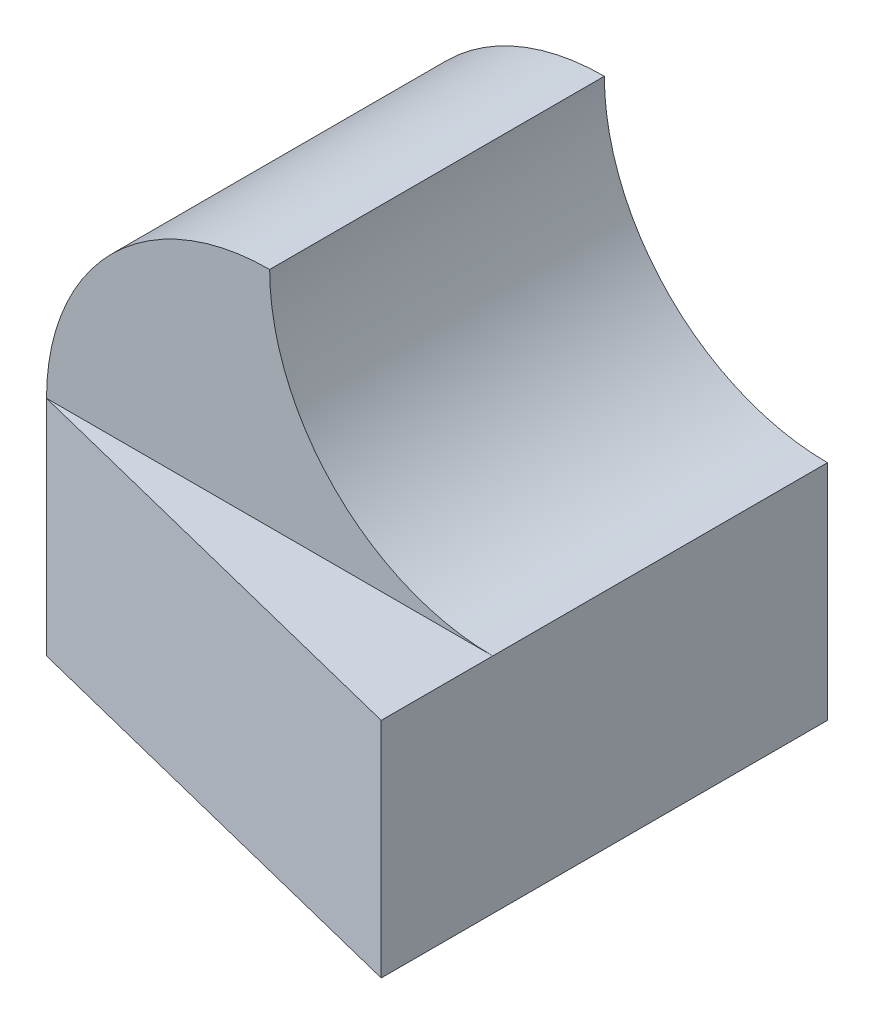
SolidWorks part; units mm, degrees
ref_plane "Front" through (0, 0, 0) normal (0, 0, 1) x (1, 0, 0)
ref_plane "Top" through (0, 0, 0) normal (0, 1, 0) x (1, 0, 0)
ref_plane "Right" through (0, 0, 0) normal (1, 0, 0) x (0, 0, -1)
sketch "Sketch1" plane through (0, 0, 0) normal (0, 0, 1) x (1, 0, 0)
  line L0 (0, 0) -> (4, 0)
  line L1 (4, 0) -> (4, 2)
  line L2 (0, 2) -> (0, 0)
  arc A0 (4, 2) -> (2, 4) centre (4, 4) cw
  arc A1 (2, 4) -> (0, 2) centre (2, 2) ccw
  point P8 (1.9827, 3.9999)
  dimension "D4" = 2
  dimension "D5" = 2
  dimension "D1" = 2
  dimension "D2" = 2
  dimension "D3" = 4
  dimension "D6" = 2
  dimension "D7" = 2
extrude "Boss-Extrude1" add sketch "Sketch1" along normal blind 3
sketch "Sketch2" plane through (0, 0, 0) normal (0, -1, 0) x (1, 0, 0)
  line L0 (0, 3) -> (4, 4)
  line L1 (4, 4) -> (4, 3)
  line L2 (4, 3) -> (0, 3)
  point P3 (4, 3.9884)
  dimension "D1" = 1
extrude "Boss-Extrude2" add sketch "Sketch2" against normal blind 2
sketch "Sketch4" plane through (0, 0, 0) normal (0, 0, -1) x (-1, 0, 0)
  line L0 (-2, 0) -> (0, 2)
  line L1 (0, 0) -> (-4, 0) construction
  line L2 (0, 2) -> (0, 0)
  line L3 (0, 0) -> (-2, 0)
  dimension "D1" = 2
extrude "Cut-Extrude1" cut sketch "Sketch4" against normal blind 1
